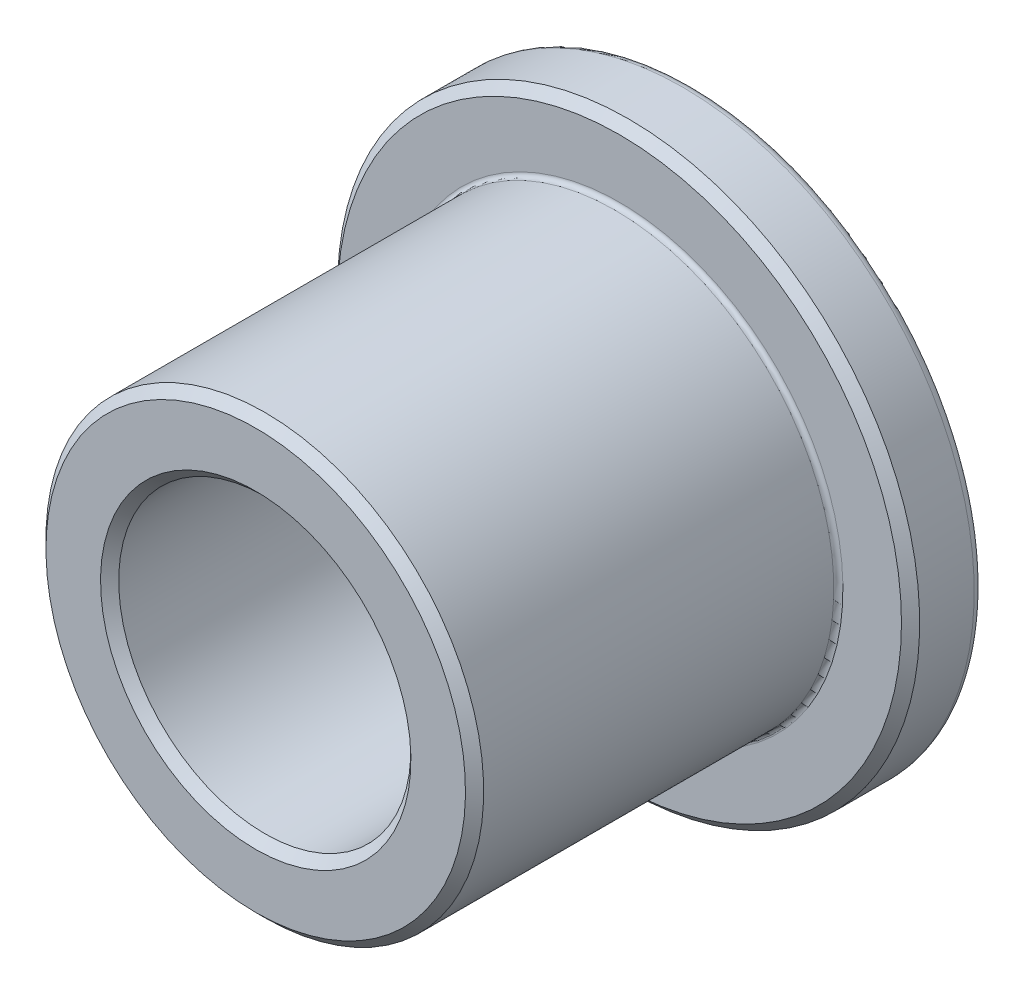
SolidWorks part; units mm, degrees
ref_plane "Front Plane" through (0, 0, 0) normal (0, 0, 1) x (1, 0, 0)
ref_plane "Top Plane" through (0, 0, 0) normal (0, 1, 0) x (1, 0, 0)
ref_plane "Right Plane" through (0, 0, 0) normal (1, 0, 0) x (0, 0, -1)
sketch "Sketch1" plane through (0, 0, 0) normal (0, 0, 1) x (1, 0, 0)
  circle A0 centre (0, 0) radius 3.1877
  circle A1 centre (0, 0) radius 4.7752
  circle A2 centre (0, 0) radius 6.35
  point P5 (0, 4.7752)
  point P6 (0, 3.1877)
  point P7 (0, 6.35)
  dimension "ID" = 6.3754
  dimension "OD" = 9.5504
  dimension "Flange OD" = 12.7
sketch "Sketch2" plane through (0, 0, 0) normal (1, 0, 0) x (0, 0, -1)
  line L0 (4.7625, 0) -> (-4.7625, 0)
  line L1 (4.7625, 0) -> (4.7625, 6.35)
  line L2 (4.7625, 6.35) -> (3.175, 6.35)
  line L3 (3.175, 6.35) -> (3.175, 4.7752)
  line L4 (3.175, 4.7752) -> (-4.7625, 4.7752)
  line L5 (-4.7625, 4.7752) -> (-4.7625, 3.1877)
  line L6 (-4.7625, 3.1877) -> (4.7625, 3.1877)
  point P4 (0, 0)
  dimension "Flange Thickness" = 1.5875
  dimension "Length" = 9.525
sketch "Sketch3" plane through (0, 0, 0) normal (1, 0, 0) x (0, 0, -1)
  line L0 (4.7625, 6.35) -> (3.175, 6.35) construction
  line L1 (3.175, 6.35) -> (3.175, 4.7752) construction
  line L2 (3.175, 4.7752) -> (-4.7625, 4.7752) construction
  line L3 (-4.7625, 3.1877) -> (4.7625, 3.1877) construction
  line L4 (-4.7625, 4.7752) -> (-4.7625, 3.1877) construction
  line L5 (4.7625, 6.35) -> (3.175, 6.35)
  line L6 (3.175, 6.35) -> (3.175, 4.7752)
  line L7 (3.175, 4.7752) -> (-4.7625, 4.7752)
  line L8 (-4.7625, 3.1877) -> (4.7625, 3.1877)
  line L9 (-4.7625, 4.7752) -> (-4.7625, 3.1877)
  line L10 (4.7625, 6.35) -> (4.7625, 3.1877)
revolve "Revolve1" add sketch "Sketch3" angle 360 about L0
chamfer "Chamfer1" distance 0.1984 angle 45 3 edges at (0, 6.35, -3.175) (0, 4.7752, 4.7625) (0, 3.1877, 4.7625)
fillet "Fillet1" radius 0.1984 1 edges at (0, 6.35, -4.7625)
fillet "Fillet2" radius 0.0992 1 edges at (0, 4.7752, -3.175)
equation "\"D1@Chamfer1\"=\"Flange Thickness@Sketch2\"*.125"
equation "\"D1@Fillet1\"=\"D1@Chamfer1\""
equation "\"D1@Fillet2\"=\"D1@Fillet1\"*.5"
